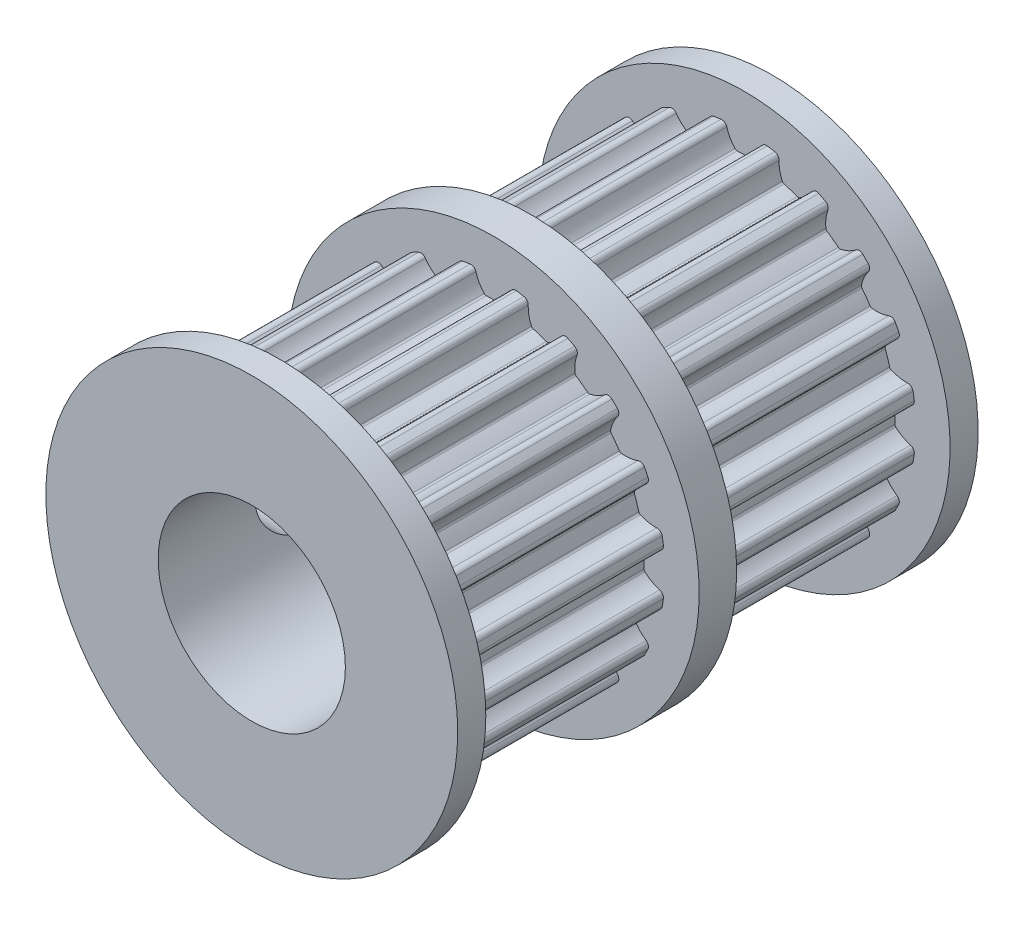
SolidWorks part; units mm, degrees
material "6061-T6 (SS)"
ref_plane "前基準面" through (0, 0, 0) normal (0, 0, 1) x (1, 0, 0)
ref_plane "上基準面" through (0, 0, 0) normal (0, 1, 0) x (1, 0, 0)
ref_plane "右基準面" through (0, 0, 0) normal (1, 0, 0) x (0, 0, -1)
sketch "草圖1" plane through (0, 0, 0) normal (0, 0, 1) x (1, 0, 0)
  circle A0 centre (0, 0) radius 9.17
  dimension "D1" = 18.34
extrude "填料-伸長1" add sketch "草圖1" along normal mid plane 24.8
sketch "草圖2" plane through (0, 0, 12.4) normal (0, 0, 1) x (1, 0, 0)
  line L0 (0, 0) -> (0, 9.17) construction
  line L1 (0, 9.17) -> (0, 9.424) construction
  line L2 (-0.975, 9.424) -> (0.975, 9.424) construction
  circle A0 centre (0, 0) radius 9.17 construction
  arc A1 (-0.3728, 8.0514) -> (0.3728, 8.0514) centre (0, 0) cw
  arc A2 (-0.3728, 8.0514) -> (-0.4911, 8.1007) centre (-0.3798, 8.2012) cw
  arc A3 (-0.4911, 8.1007) -> (-0.9252, 8.8857) centre (0.975, 9.424) cw
  arc A4 (-1.2322, 9.0868) -> (-0.9252, 8.8857) centre (-1.1946, 8.8094) cw
  arc A5 (0.3728, 8.0514) -> (0.4911, 8.1007) centre (0.3798, 8.2012) ccw
  arc A6 (0.4911, 8.1007) -> (0.9252, 8.8857) centre (-0.975, 9.424) ccw
  arc A7 (1.2322, 9.0868) -> (0.9252, 8.8857) centre (1.1946, 8.8094) ccw
  arc A8 (-1.2322, 9.0868) -> (1.2322, 9.0868) centre (0, 0) cw
  dimension "D1" = 0.15
  dimension "D2" = 1.975
  dimension "D3" = 0.28
  dimension "D4" = 1.11
  dimension "D5" = 0.254
  dimension "D6" = 1.95
extrude "除料-伸長1" cut sketch "草圖2" against normal through all and the other way through all
pattern_circular "環狀複製排列1" count 20 over 360 about axis through (0, 0, 0) along (0, 0, 1) of "除料-伸長1"
sketch "草圖3" plane through (0, 0, 12.4) normal (0, 0, 1) x (1, 0, 0)
  circle A0 centre (0, 0) radius 11
  dimension "D1" = 22
extrude "填料-伸長2" add sketch "草圖3" along normal blind 1.5
sketch "草圖9" plane through (0, 0, -12.4) normal (0, 0, -1) x (-1, 0, 0)
  circle A0 centre (0, 0) radius 11
  circle A1 centre (0, 0) radius 11 construction
extrude "填料-伸長3" add sketch "草圖9" along normal blind 1.5
sketch "草圖12" plane through (0, 0, 12.4) normal (0, 0, 1) x (1, 0, 0)
  circle A0 centre (0, 0) radius 11
  dimension "D1" = 22
extrude "填料-伸長4" add sketch "草圖12" along normal mid plane 2 from offset 12.4 offset against normal yes
sketch "草圖4" plane through (0, 0, 13.9) normal (0, 0, 1) x (1, 0, 0)
  circle A0 centre (0, 0) radius 5
  dimension "D1" = 10
extrude "除料-伸長2" cut sketch "草圖4" against normal through all
sketch "草圖11" plane through (0, 0, 0) normal (1, 0, 0) x (0, 0, -1)
  line L0 (6.6, 0) -> (0, 0) construction
  line L1 (0, 0) -> (-6.6, 0) construction
  circle A1 centre (6.6, 0) radius 2.1
  circle A2 centre (-6.6, 0) radius 2.1
  dimension "D1" = 6.6
  dimension "D3" = 4.2
  dimension "D2" = 6.6
extrude "除料-伸長4" cut sketch "草圖11" against normal through all
